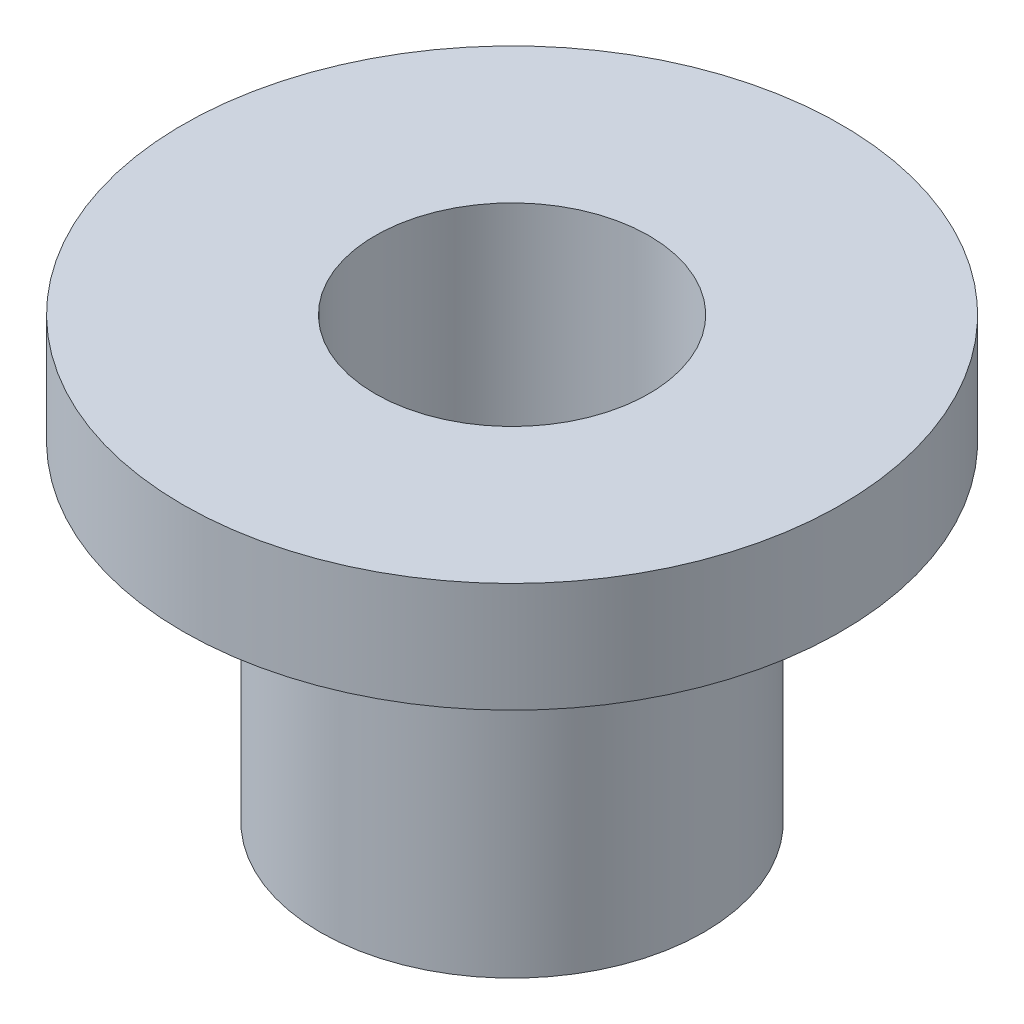
SolidWorks part; units mm, degrees
material "Rubber"
ref_plane "Front Plane" through (0, 0, 0) normal (0, 0, 1) x (1, 0, 0)
ref_plane "Top Plane" through (0, 0, 0) normal (0, 1, 0) x (1, 0, 0)
ref_plane "Right Plane" through (0, 0, 0) normal (1, 0, 0) x (0, 0, -1)
sketch "Sketch1" plane through (0, 0, 0) normal (0, 0, 1) x (1, 0, 0)
  line L0 (0, 0) -> (0, -12.7) construction
  line L1 (0, -55) -> (0, 55) construction
  line L2 (55, 0) -> (-55, 0) construction
  line L3 (-9.525, 0) -> (-3.9624, 0)
  line L4 (-9.525, 0) -> (-9.525, -3.175)
  line L5 (-9.525, -3.175) -> (-5.5499, -3.175)
  line L6 (-3.9624, 0) -> (-3.9624, -12.7)
  line L8 (-5.5499, -3.175) -> (-5.5499, -12.7)
  line L9 (-5.5499, -12.7) -> (-3.9624, -12.7)
  dimension "D1" = 7.9248
  dimension "D2" = 12.7
  dimension "D3" = 3.175
  dimension "D4" = 1.5875
  dimension "D5" = 19.05
revolve "Revolve1" add sketch "Sketch1" angle 360 about L0
